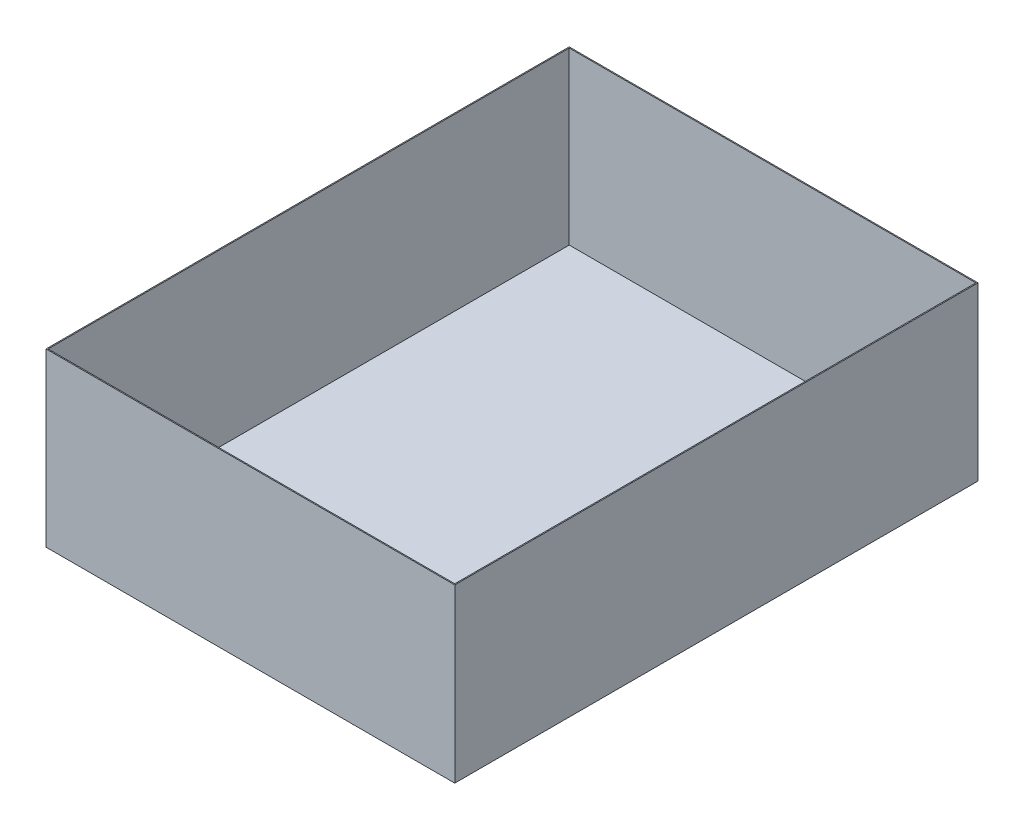
SolidWorks part; units mm, degrees
material "6061 Alloy"
ref_plane "Front Plane" through (0, 0, 0) normal (0, 0, 1) x (1, 0, 0)
ref_plane "Top Plane" through (0, 0, 0) normal (0, 1, 0) x (1, 0, 0)
ref_plane "Right Plane" through (0, 0, 0) normal (1, 0, 0) x (0, 0, -1)
sketch "Sketch1" plane through (0, 0, 0) normal (0, 1, 0) x (1, 0, 0)
  line L0 (125, 320) -> (125, 354.3543) construction
  line L1 (0, 320) -> (250, 320)
  line L2 (0, 320) -> (0, 0)
  line L3 (0, 0) -> (250, 0)
  line L4 (250, 320) -> (250, 0)
  line L5 (91.9749, 345.5599) -> (158.0251, 345.5599)
  line L6 (91.9749, 345.5599) -> (91.9749, 320)
  line L8 (158.0251, 345.5599) -> (158.0251, 320)
  line L9 (250, 160) -> (0, 160) construction
  line L11 (158.0251, -25.5599) -> (158.0251, 0)
  line L12 (91.9749, -25.5599) -> (158.0251, -25.5599)
  line L13 (91.9749, -25.5599) -> (91.9749, 0)
  point P9 (125, 345.5599)
  dimension "length" = 250
  dimension "width" = 320
extrude "Boss-Extrude5" add sketch "Sketch1" against normal blind 105 contours L4 L1 L2 L3
shell "Shell2" thickness 0.635
